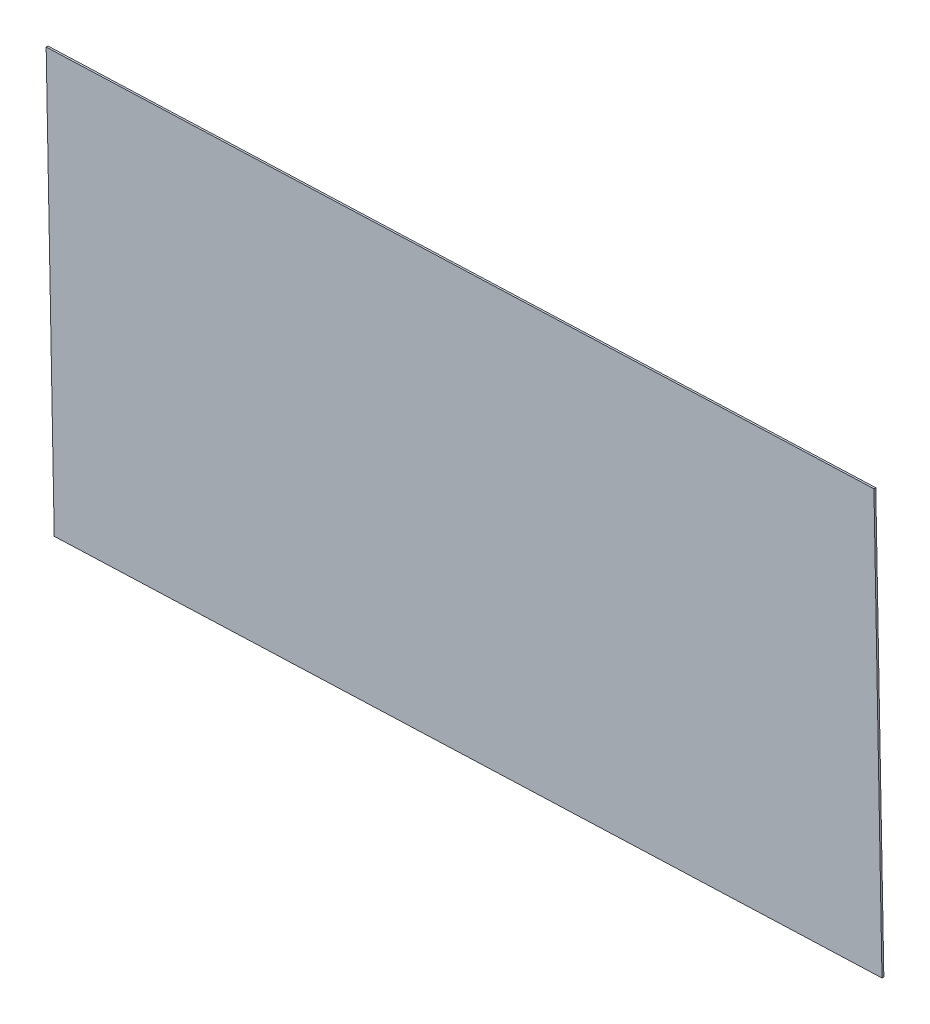
SolidWorks part; units mm, degrees
material "Balsa"
ref_plane "Front Plane" through (0, 0, 0) normal (0, 0, 1) x (1, 0, 0)
ref_plane "Top Plane" through (0, 0, 0) normal (0, 1, 0) x (1, 0, 0)
ref_plane "Right Plane" through (0, 0, 0) normal (1, 0, 0) x (0, 0, -1)
sketch "Sketch1" plane through (7.1771, -2.348, -45.8981) normal (0.0103, 0.0088, 0.9999) x (0.9996, 0.0278, -0.0105)
  line L0 (0, 0) -> (-352.4535, 0) construction
  line L1 (-611.0518, 611.2) -> (788.9482, 611.2)
  line L2 (-611.0518, 611.2) -> (-611.0518, -100)
  line L3 (-611.0518, -100) -> (788.9482, -100)
  line L4 (788.9482, 611.2) -> (788.9482, -100)
  dimension "D1" = 711.2
  dimension "D2" = 1400
  dimension "D3" = 100
  dimension "D4" = 30
extrude "Boss-Extrude1" add sketch "Sketch1" against normal blind 3.175
